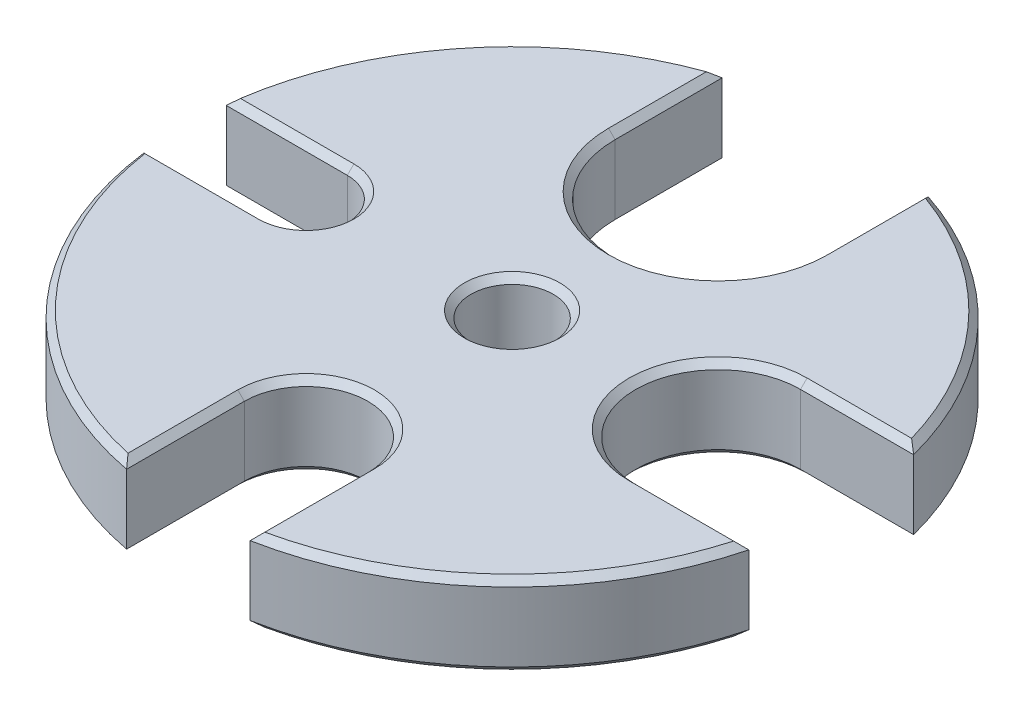
SolidWorks part; units mm, degrees
ref_plane "Front Plane" through (0, 0, 0) normal (0, 0, 1) x (1, 0, 0)
ref_plane "Top Plane" through (0, 0, 0) normal (0, 1, 0) x (1, 0, 0)
ref_plane "Right Plane" through (0, 0, 0) normal (1, 0, 0) x (0, 0, -1)
sketch "Sketch1" plane through (0, 0, 0) normal (0, 1, 0) x (1, 0, 0)
  line L0 (-2.5, 0.5) -> (-3.9686, 0.5)
  line L1 (-2.5, -0.5) -> (-3.9686, -0.5)
  line L2 (-1.25, 2.5) -> (-1.25, 3.7997)
  line L4 (1.25, 3.7997) -> (1.25, 2.5)
  line L5 (2.5, 1) -> (3.873, 1)
  line L7 (3.873, -1) -> (2.5, -1)
  line L8 (-0.75, -2.5) -> (-0.75, -3.9291)
  line L10 (0.75, -3.9291) -> (0.75, -2.5)
  circle A0 centre (0, 0) radius 2.5 construction
  arc A1 (-1.25, 3.7997) -> (-3.9686, 0.5) centre (0, 0) ccw
  arc A2 (-1.25, 2.5) -> (1.25, 2.5) centre (0, 2.5) ccw
  arc A3 (2.5, 1) -> (2.5, -1) centre (2.5, 0) ccw
  arc A4 (0.75, -2.5) -> (-0.75, -2.5) centre (0, -2.5) ccw
  arc A5 (-2.5, -0.5) -> (-2.5, 0.5) centre (-2.5, 0) ccw
  arc A6 (3.873, 1) -> (1.25, 3.7997) centre (0, 0) ccw
  arc A7 (0.75, -3.9291) -> (3.873, -1) centre (0, 0) ccw
  arc A8 (-3.9686, -0.5) -> (-0.75, -3.9291) centre (0, 0) ccw
  circle A9 centre (0, 0) radius 0.5
  dimension "D1" = 5
  dimension "D2" = 8
  dimension "D3" = 2.5
  dimension "D4" = 2
  dimension "D5" = 1.5
  dimension "D6" = 1
  dimension "D7" = 1
extrude "Boss-Extrude1" add sketch "Sketch1" along normal mid plane 1
chamfer "Chamfer1" distance 0.08 angle 45 17 edges at (0, 0.5, 0.5) (-1.25, 0.5, -3.1498) (0, 0.5, -1.25) (1.25, 0.5, -3.1498) (2.919, 0.5, -2.7348) (3.1865, 0.5, -1) (1.5, 0.5, 0) (3.1865, 0.5, 1) (2.7364, 0.5, 2.9176) (0.75, 0.5, 3.2145) (0, 0.5, 1.75) (-0.75, 0.5, 3.2145) (-2.9165, 0.5, 2.7375) (-3.2343, 0.5, 0.5) (-2, 0.5, 0) (-3.2343, 0.5, -0.5) (-3.0871, 0.5, -2.5435)
chamfer "Chamfer2" distance 0.08 angle 45 17 edges at (0, -0.5, 0.5) (-3.2343, -0.5, -0.5) (-2, -0.5, 0) (-3.2343, -0.5, 0.5) (-2.9165, -0.5, 2.7375) (-0.75, -0.5, 3.2145) (0, -0.5, 1.75) (0.75, -0.5, 3.2145) (2.7364, -0.5, 2.9176) (3.1865, -0.5, 1) (1.5, -0.5, 0) (3.1865, -0.5, -1) (2.919, -0.5, -2.7348) (1.25, -0.5, -3.1498) (0, -0.5, -1.25) (-1.25, -0.5, -3.1498) (-3.0871, -0.5, -2.5435)
